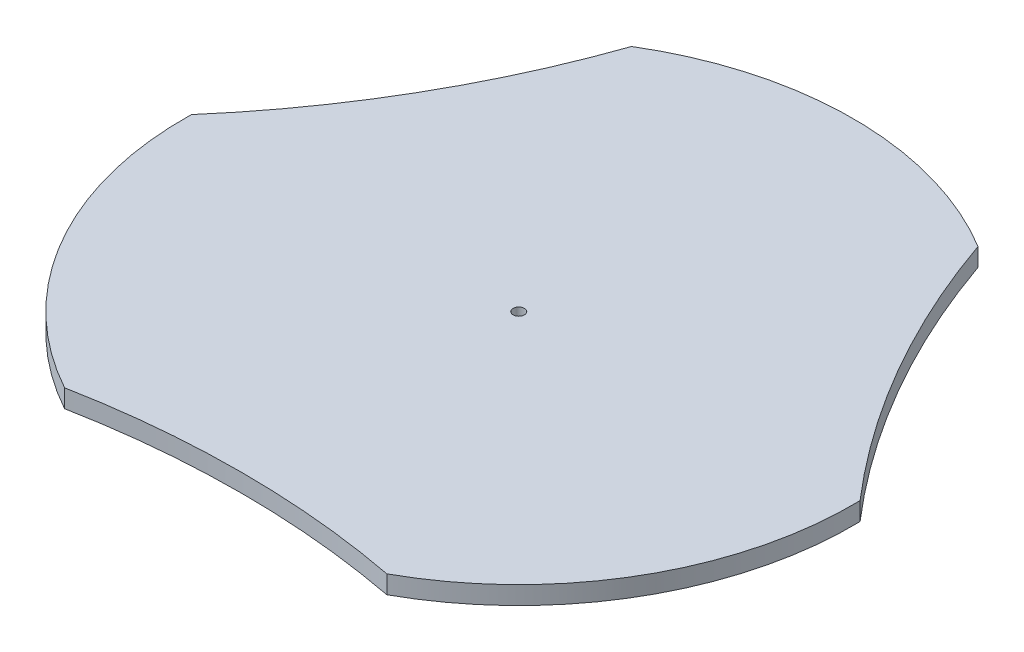
SolidWorks part; units mm, degrees
ref_plane "Front Plane" through (0, 0, 0) normal (0, 0, 1) x (1, 0, 0)
ref_plane "Top Plane" through (0, 0, 0) normal (0, 1, 0) x (1, 0, 0)
ref_plane "Right Plane" through (0, 0, 0) normal (1, 0, 0) x (0, 0, -1)
sketch "Sketch1" plane through (0, 0, 0) normal (0, 1, 0) x (1, 0, 0)
  circle A0 centre (0, 0) radius 37
  dimension "D1" = 74
extrude "Boss-Extrude1" add sketch "Sketch1" along normal blind 1.6
sketch "Sketch3" plane through (0, 1.6, 0) normal (0, 1, 0) x (1, 0, 0)
  line L0 (0, 0) -> (-17101.0072, 46984.631) construction
  line L1 (0, 0) -> (17101.0072, 46984.631) construction
  line L2 (0, 0) -> (0, 50000) construction
  line L3 (-12.6547, 34.7686) -> (-9.9186, 27.2511) construction
  line L4 (12.6547, 34.7686) -> (9.9186, 27.2511) construction
  line L5 (23.7831, -28.3436) -> (18.6408, -22.2153) construction
  line L6 (36.4379, -6.425) -> (28.5594, -5.0358) construction
  line L7 (-36.4379, -6.425) -> (-28.5594, -5.0358) construction
  line L8 (-23.7831, -28.3436) -> (-18.6408, -22.2153) construction
  line L9 (2.789, 31.8782) -> (0, 0) construction
  arc A0 (-12.6547, 34.7686) -> (12.6547, 34.7686) centre (0, 0) cw construction
  circle A1 centre (0, 0) radius 37 construction
  arc A2 (-9.9186, 27.2511) -> (9.9186, 27.2511) centre (0, 0) cw construction
  circle A3 centre (2.789, 31.8782) radius 1.75
  arc A4 (28.5594, -5.0358) -> (18.6408, -22.2153) centre (0, 0) cw construction
  arc A5 (36.4379, -6.425) -> (23.7831, -28.3436) centre (0, 0) cw construction
  circle A6 centre (26.2129, -18.3544) radius 1.75
  arc A7 (-18.6408, -22.2153) -> (-28.5594, -5.0358) centre (0, 0) cw construction
  arc A8 (-23.7831, -28.3436) -> (-36.4379, -6.425) centre (0, 0) cw construction
  circle A9 centre (-29.0018, -13.5238) radius 1.75
  point P33 (0, 0)
  dimension "D5" = 3.5
  dimension "D1" = 20
  dimension "D2" = 20
  dimension "D3" = 8
  dimension "D6" = 32
  dimension "D7" = 5
  dimension "D4" = 3
sketch "Sketch5" plane through (0, 1.6, 0) normal (0, 1, 0) x (1, 0, 0)
  circle A0 centre (86.6025, 50) radius 75.5001
  dimension "D1" = 100
extrude "Cut-Extrude2" cut sketch "Sketch5" against normal through all
sketch "Sketch7" plane through (0, 1.6, 0) normal (0, 1, 0) x (1, 0, 0)
  circle A0 centre (0, 0) radius 0.5
  dimension "D1" = 1
extrude "Cut-Extrude3" cut sketch "Sketch7" against normal through all
extrude "Cut-Extrude4" cut sketch "Sketch3" against normal through all
sketch "Sketch8" plane through (0, 1.6, 0) normal (0, 1, 0) x (1, 0, 0)
  line L0 (-14.2641, 35.0556) -> (47112.9297, 8344.8514) construction
  line L1 (-6.5986, 37.4227) -> (-11.9778, 36.4742) construction
  line L2 (-5.904, 33.4835) -> (0, 0) construction
  line L3 (0, -1000) -> (0, 49000) construction
  circle A0 centre (-5.904, 33.4835) radius 4 construction
  arc A1 (12.6547, 34.7686) -> (36.4379, -6.425) centre (0, 0) ccw construction
  circle A2 centre (-5.904, 33.4835) radius 1.65
  dimension "D1" = 8
  dimension "D3" = 3.3
  dimension "D2" = 1
  dimension "D4" = 10
extrude "Cut-Extrude5" cut sketch "Sketch8" against normal through all
pattern_circular "CirPattern2" count 3 over 360 about axis through (0, 0, 0) along (0, 1, 0) of "Cut-Extrude2", "Cut-Extrude5"
sketch "Sketch9" plane through (0, 1.6, 0) normal (0, 1, 0) x (1, 0, 0)
  line L1 (-36.4379, -28.3436) -> (36.4379, -28.3436)
  line L2 (-36.4379, -28.3436) -> (-36.4379, 37)
  line L3 (-36.4379, 37) -> (36.4379, 37)
  line L4 (36.4379, -28.3436) -> (36.4379, 37)
  arc A0 (12.6547, 34.7686) -> (-12.6547, 34.7686) centre (0, 0) ccw construction
  dimension "D1" = 72.8758
  dimension "D2" = 65.3436
sketch "Sketch10" plane through (0, 1.6, 0) normal (0, 1, 0) x (1, 0, 0)
  circle A0 centre (0, 0) radius 29.5
  dimension "D1" = 59
extrude "Cut-Extrude7" cut sketch "Sketch10" against normal blind 10 flip side to cut
sketch "Sketch11" plane through (0, 1.6, 0) normal (0, 1, 0) x (1, 0, 0)
  line L0 (-29.4936, -988.4588) -> (-29.4936, 49011.5412) construction
  line L1 (29.4936, -998.5133) -> (29.4936, 49001.4867) construction
  line L2 (-1012.334, 29.5) -> (48987.666, 29.5) construction
  line L3 (-1020.8898, -25.8499) -> (48979.1102, -25.8499) construction
  line L5 (-29.4936, 29.5) -> (29.4936, 29.5)
  line L6 (-29.4936, 29.5) -> (-29.4936, -25.8499)
  line L7 (-29.4936, -25.8499) -> (29.4936, -25.8499)
  line L8 (29.4936, 29.5) -> (29.4936, -25.8499)
  arc A0 (15.2798, 25.2345) -> (-15.2798, 25.2345) centre (0, 0) ccw construction
  dimension "D1" = 58.9872
  dimension "D2" = 55.3499
